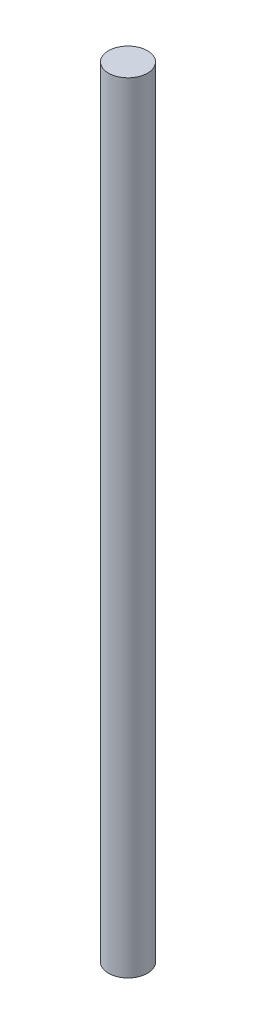
SolidWorks part; units mm, degrees
material "Chrome Stainless Steel"
ref_plane "Front Plane" through (0, 0, 0) normal (0, 0, 1) x (1, 0, 0)
ref_plane "Top Plane" through (0, 0, 0) normal (0, 1, 0) x (1, 0, 0)
ref_plane "Right Plane" through (0, 0, 0) normal (1, 0, 0) x (0, 0, -1)
sketch "Sketch1" plane through (0, 0, 0) normal (0, 1, 0) x (1, 0, 0)
  circle A0 centre (0, 0) radius 10
  dimension "D1" = 20
extrude "Boss-Extrude1" add sketch "Sketch1" along normal blind 400
